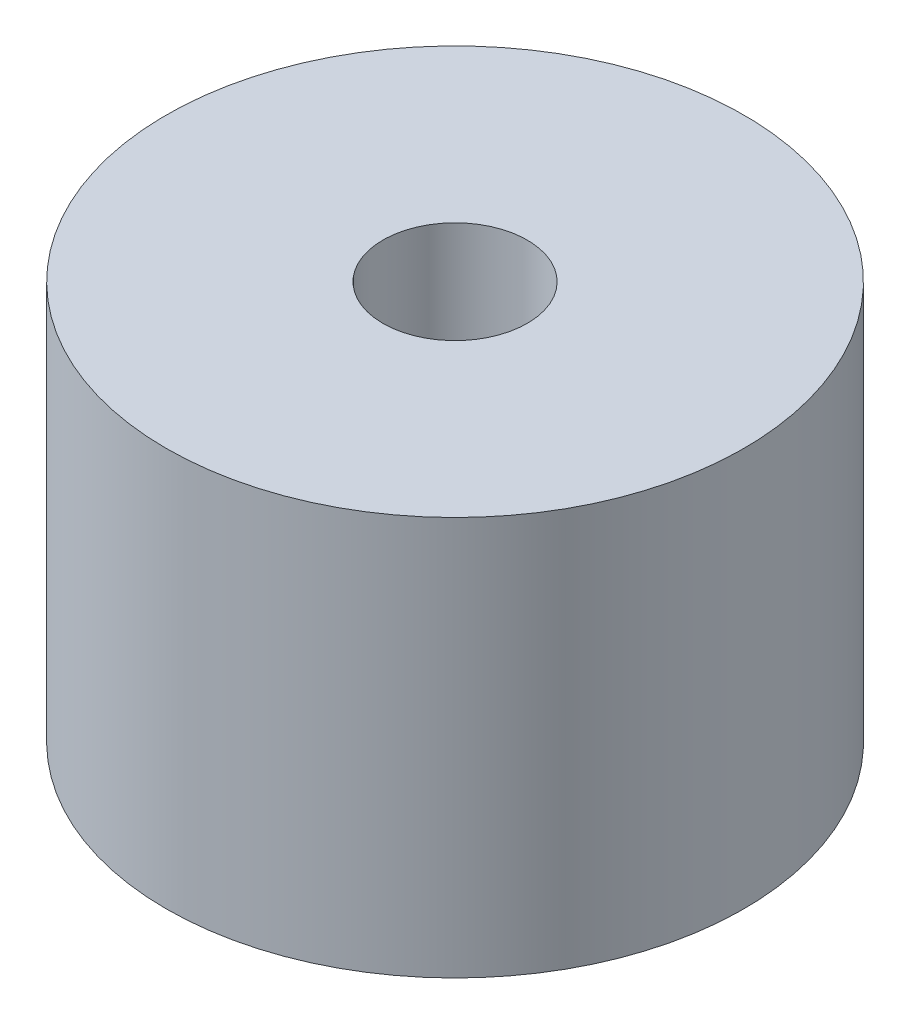
SolidWorks part; units mm, degrees
ref_plane "Front Plane" through (0, 0, 0) normal (0, 0, 1) x (1, 0, 0)
ref_plane "Top Plane" through (0, 0, 0) normal (0, 1, 0) x (1, 0, 0)
ref_plane "Right Plane" through (0, 0, 0) normal (1, 0, 0) x (0, 0, -1)
sketch "Sketch1" plane through (0, 0, 0) normal (0, 1, 0) x (1, 0, 0)
  circle A0 centre (0, 0) radius 4.2
  dimension "D1" = 8.4
extrude "Boss-Extrude1" add sketch "Sketch1" along normal mid plane 5.8 contours A0
hole_wizard "M3x0.5 Tapped Hole1" positions "Sketch2" profile "Sketch3" tap size "M3x0.5" standard "ANSI Metric" end condition through all
sketch "Sketch2" plane through (0, 2.9, 0) normal (0, 1, 0) x (1, 0, 0)
  point P1 (0, 0)
sketch "Sketch3" plane through (0, 2.9, 0) normal (1, 0, 0) x (0, 0, 1)
  line L0 (0, 0) -> (0, 5.8)
  line L1 (0, 5.8) -> (1.05, 5.8)
  line L2 (1.05, 5.8) -> (1.05, 0)
  line L5 (1.05, 0) -> (0, 0)
  line L11 (0, -6.35) -> (0, 107.95) construction
  dimension "Thread Major Dia." = 2.1
  dimension "Thru Tap Drill Depth" = 5.8
